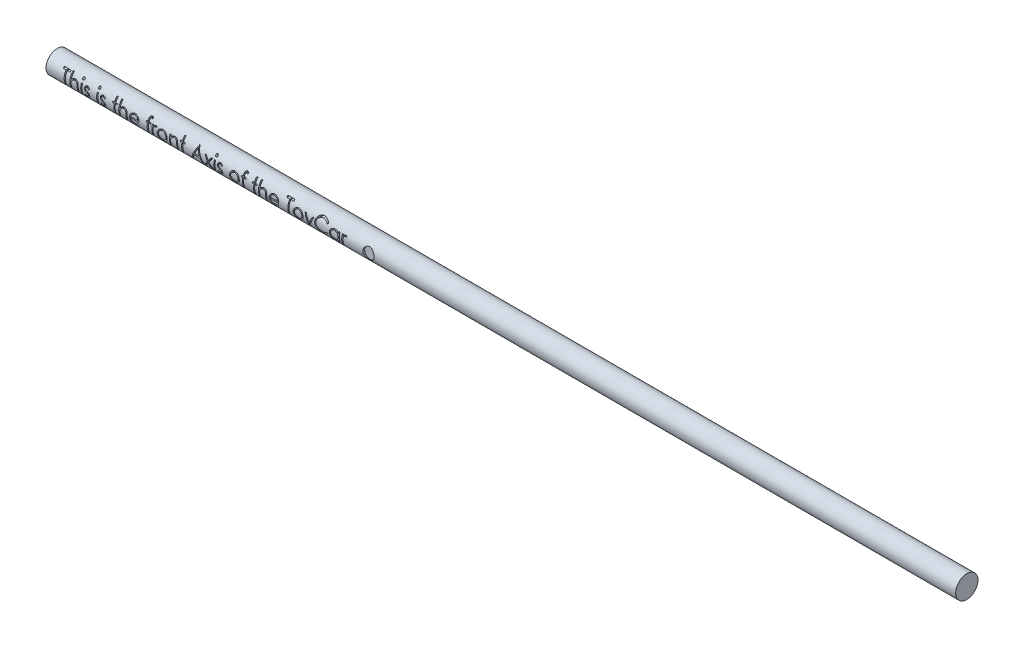
SolidWorks part; units mm, degrees
ref_plane "Front Plane" through (0, 0, 0) normal (0, 0, 1) x (1, 0, 0)
ref_plane "Top Plane" through (0, 0, 0) normal (0, 1, 0) x (1, 0, 0)
ref_plane "Right Plane" through (0, 0, 0) normal (1, 0, 0) x (0, 0, -1)
sketch "Sketch1" plane through (0, 0, 0) normal (1, 0, 0) x (0, 0, -1)
  circle A0 centre (0, 0) radius 3
extrude "Boss-Extrude1" add sketch "Sketch1" along normal blind 244
sketch "Sketch2" plane through (0, 0, 0) normal (0, 0, 1) x (1, 0, 0)
  text T0 "This is the front Axis of the ToyCar"
extrude "Cut-Extrude1" cut sketch "Sketch2" along normal through all
ref_plane "Plane1" through (0, 0, 2.5) normal (0, 0, 1) x (1, 0, 0)
sketch "Sketch3" plane through (0, 0, 2.5) normal (0, 0, 1) x (1, 0, 0)
  line L0 (3.3, 0) -> (-3.3, 0) construction
  circle A0 centre (86.4946, 0) radius 1.5
extrude "Cut-Extrude2" cut sketch "Sketch3" along normal blind 1 contours A0
